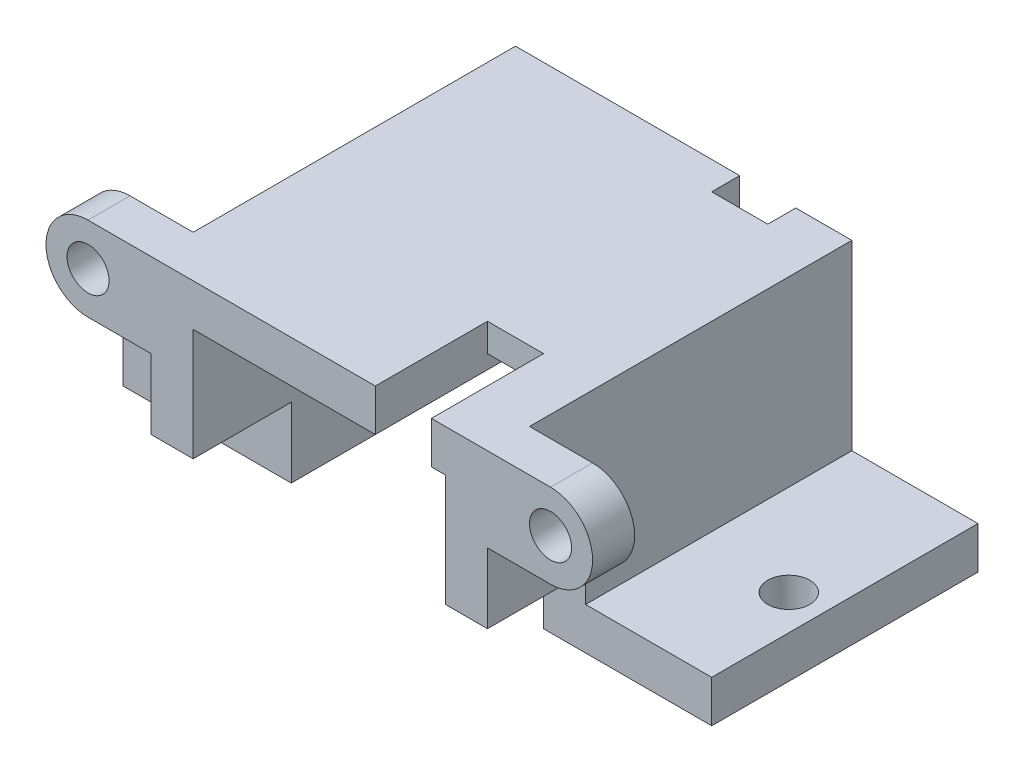
SolidWorks part; units mm, degrees
material "PVC 0.007 plastifié"
ref_plane "Face" through (0, 0, 0) normal (0, 0, 1) x (1, 0, 0)
ref_plane "Dessus" through (0, 0, 0) normal (0, 1, 0) x (1, 0, 0)
ref_plane "Droite" through (0, 0, 0) normal (1, 0, 0) x (0, 0, -1)
sketch "Esquisse1" plane through (0, 0, 0) normal (0, 0, 1) x (1, 0, 0)
  line L0 (-21, 0) -> (-9, 0)
  line L1 (-9, 0) -> (-9, 13)
  line L2 (-9, 13) -> (9, 13)
  line L3 (9, 13) -> (9, 0)
  line L4 (9, 0) -> (21, 0)
  line L5 (0, 0) -> (0, 35.9745) construction
  dimension "D1" = 42
  dimension "D2" = 18
  dimension "D3" = 13
extrude "Extru.-Mince1" add sketch "Esquisse1" along normal mid plane 26 thin thin type one direction reverse wall 3
sketch "Esquisse2" plane through (0, 0, 13) normal (0, 0, 1) x (1, 0, 0)
  line L0 (-12, 16) -> (-16.5, 16)
  line L2 (-16.5, 10) -> (-12, 10)
  line L3 (-12, 10) -> (-12, 16)
  line L4 (-12, 16) -> (12, 16) construction
  arc A0 (-16.5, 10) -> (-16.5, 16) centre (-16.5, 13) cw
  dimension "D1" = 6
  dimension "D2" = 4.5
extrude "Extrusion1" add sketch "Esquisse2" against normal blind 3
sketch "Esquisse3" plane through (0, 0, 13) normal (0, 0, 1) x (1, 0, 0)
  circle A0 centre (-16.5, 13) radius 1.5
  arc A1 (-16.5, 16) -> (-16.5, 10) centre (-16.5, 13) ccw construction
  dimension "D1" = 3
extrude "Enlèv. mat.-Extru.1" cut sketch "Esquisse3" against normal up to next (3 mm away)
mirror "Symétrie1" about plane through (0, 0, 0) normal (1, 0, 0) of "Extrusion1", "Enlèv. mat.-Extru.1"
sketch "Esquisse4" plane through (0, 16, 0) normal (0, 1, 0) x (1, 0, 0)
  line L0 (-16.5, -13) -> (16.5, -13) construction
  line L1 (8, -13) -> (4, -13)
  line L2 (8, -13) -> (8, -5)
  line L3 (8, -5) -> (4, -5)
  line L4 (4, -13) -> (4, -5)
  line L5 (-12, 13) -> (12, 13) construction
  line L6 (4, 13) -> (8, 13)
  line L7 (4, 13) -> (4, 11)
  line L8 (4, 11) -> (8, 11)
  line L9 (8, 13) -> (8, 11)
  line L10 (12, -10) -> (12, 13) construction
  dimension "D1" = 8
  dimension "D2" = 4
  dimension "D3" = 2
  dimension "D4" = 4
  dimension "D5" = 4
  dimension "D6" = 4
extrude "Enlèv. mat.-Extru.2" cut sketch "Esquisse4" against normal up to next
sketch "Esquisse6" plane through (21, 0, 0) normal (1, 0, 0) x (0, 0, -1)
  line L0 (-13, 3) -> (-13, 0) construction
  line L1 (-13, 0) -> (-6, 0)
  line L2 (-13, 0) -> (-13, 5)
  line L3 (-13, 5) -> (-6, 5)
  line L4 (-6, 0) -> (-6, 5)
  line L5 (-13, 0) -> (13, 0) construction
  dimension "D1" = 7
  dimension "D2" = 5
extrude "Enlèv. mat.-Extru.4" cut sketch "Esquisse6" against normal up to surface (42 mm away) up to face at (-21, 1.5, 0)
sketch "Esquisse7" plane through (0, 3, 0) normal (0, 1, 0) x (1, 0, 0)
  line L1 (21, -6) -> (21, 13) construction
  line L3 (21, -6) -> (12, -6) construction
  circle A1 centre (18.5, 2) radius 1.5
  point P0 (16.5, -6)
  dimension "D1" = 8
  dimension "D2" = 3
  dimension "D5" = 2.5
extrude "Enlèv. mat.-Extru.5" cut sketch "Esquisse7" against normal up to next (3 mm away)
mirror "Symétrie2" about plane through (0, 0, 0) normal (1, 0, 0) of "Enlèv. mat.-Extru.5"
sketch "Esquisse8" plane through (0, 13, 0) normal (0, -1, 0) x (1, 0, 0)
  line L1 (8, 5) -> (4, 5)
  line L2 (8, 5) -> (8, -11)
  line L3 (8, -11) -> (4, -11)
  line L4 (4, 5) -> (4, -11)
extrude "Enlèv. mat.-Extru.6" cut sketch "Esquisse8" against normal blind 1
